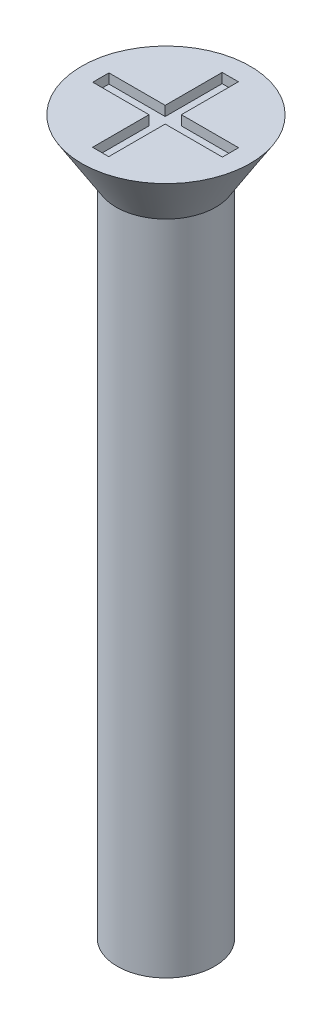
SolidWorks part; units mm, degrees
material "AISI 304"
ref_plane "Front" through (0, 0, 0) normal (0, 0, 1) x (1, 0, 0)
ref_plane "Top" through (0, 0, 0) normal (0, 1, 0) x (1, 0, 0)
ref_plane "Right" through (0, 0, 0) normal (1, 0, 0) x (0, 0, -1)
sketch "Sketch1" plane through (0, 0, 0) normal (0, 1, 0) x (1, 0, 0)
  circle A0 centre (0, 0) radius 1.5
  dimension "D1" = 3
extrude "Boss-Extrude1" add sketch "Sketch1" along normal blind 22
sketch "Sketch2" plane through (0, 22, 0) normal (0, 1, 0) x (1, 0, 0)
  circle A0 centre (0, 0) radius 2.6
  dimension "D1" = 5.2
extrude "Boss-Extrude2" add sketch "Sketch2" against normal blind 1.7 draft 32
sketch "Sketch3" plane through (0, 22, 0) normal (0, 1, 0) x (1, 0, 0)
  line L1 (-2, 0.2416) -> (2, 0.2416)
  line L2 (-2, 0.2416) -> (-2, -0.2584)
  line L3 (-2, -0.2584) -> (2, -0.2584)
  line L4 (2, 0.2416) -> (2, -0.2584)
  line L5 (-0.2653, 2) -> (0.2347, 2)
  line L6 (-0.2653, 2) -> (-0.2653, -2)
  line L7 (-0.2653, -2) -> (0.2347, -2)
  line L8 (0.2347, 2) -> (0.2347, -2)
  circle A0 centre (0, 0) radius 2.6 construction
  dimension "D1" = 0.5
  dimension "D2" = 0.5
  dimension "D3" = 4
  dimension "D4" = 4
  dimension "D5" = 2
  dimension "D6" = 2
extrude "Cut-Extrude1" cut sketch "Sketch3" against normal blind 0.3 contours L8 L5 L6 L1 | L8 L3 L6 L7 | L6 L1 L2 L3 | L1 L8 L3 L4 | L8 L1 L6 L3
